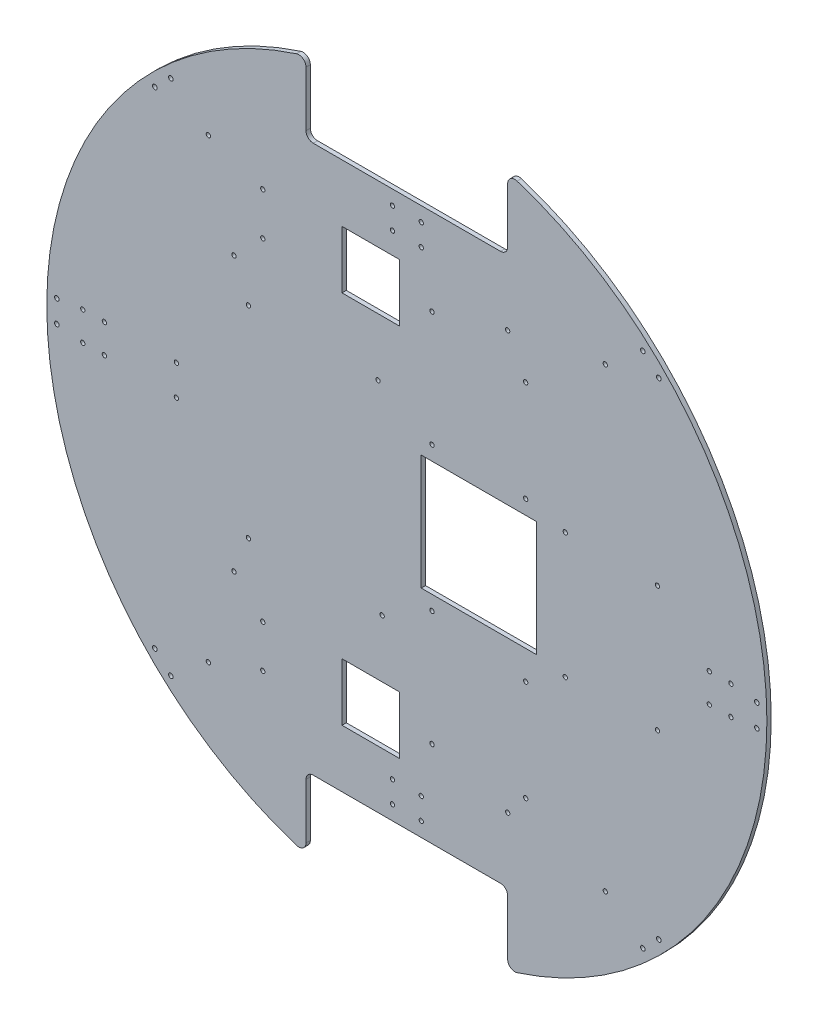
SolidWorks part; units mm, degrees
material "ｱｸﾘﾙ (中-上級の耐衝撃性)"
ref_plane "正面" through (0, 0, 0) normal (0, 0, 1) x (1, 0, 0)
ref_plane "平面" through (0, 0, 0) normal (0, 1, 0) x (1, 0, 0)
ref_plane "右側面" through (0, 0, 0) normal (1, 0, 0) x (0, 0, -1)
sketch "ｽｹｯﾁ1" plane through (0, 0, 0) normal (0, 0, 1) x (1, 0, 0)
  line L0 (0, -250) -> (0, 250) construction
  line L1 (-250, 0) -> (250, 0) construction
  circle A0 centre (0, 0) radius 250
  dimension "D1" = 500
extrude "ﾎﾞｽ - 押し出し1" add sketch "ｽｹｯﾁ1" against normal blind 3
sketch "ｽｹｯﾁ2" plane through (0, 0, 0) normal (0, 0, 1) x (1, 0, 0)
  line L0 (0, 250) -> (0, -250) construction
  line L1 (-250, 0) -> (250, 0) construction
  line L2 (0, 190) -> (52.533, 190) construction
  line L3 (0, 190) -> (-70, 190) construction
  line L5 (0, 190) -> (70, 190)
  line L7 (0, 250) -> (70, 250)
  line L8 (70, 190) -> (70, 250)
  line L9 (0, 190) -> (-70, 190)
  line L11 (0, 250) -> (-70, 250)
  line L12 (-70, 190) -> (-70, 250)
  circle A0 centre (0, 0) radius 250 construction
  dimension "D1" = 140
  dimension "D2" = 60
  dimension "D3" = 70
  dimension "D4" = 190
extrude "ｶｯﾄ - 押し出し1" cut sketch "ｽｹｯﾁ2" against normal through all
sketch "ｽｹｯﾁ3" plane through (0, 0, 0) normal (0, 0, 1) x (1, 0, 0)
  line L0 (0, 190) -> (0, -250) construction
  line L1 (-70, 190) -> (70, 190) construction
  line L2 (-250, 0) -> (250, 0) construction
  line L3 (-61.1353, -190) -> (70, -190) construction
  line L5 (0, -250) -> (70, -250)
  line L7 (0, -190) -> (70, -190)
  line L8 (70, -250) -> (70, -190)
  line L9 (0, -250) -> (-70, -250)
  line L11 (0, -190) -> (-70, -190)
  line L12 (-70, -250) -> (-70, -190)
  arc A0 (-70, 240) -> (70, 240) centre (0, 0) ccw construction
  dimension "D1" = 190
  dimension "D2" = 140
  dimension "D4" = 60
extrude "ｶｯﾄ - 押し出し2" cut sketch "ｽｹｯﾁ3" against normal through all
fillet "ﾌｨﾚｯﾄ1" radius 5 1 edges at (-70, 240, -1.5)
fillet "ﾌｨﾚｯﾄ2" radius 5 1 edges at (70, 240, -1.5)
fillet "ﾌｨﾚｯﾄ3" radius 5 1 edges at (70, 190, -1.5)
fillet "ﾌｨﾚｯﾄ4" radius 5 1 edges at (-70, 190, -1.5)
fillet "ﾌｨﾚｯﾄ5" radius 5 1 edges at (-70, -240, -1.5)
fillet "ﾌｨﾚｯﾄ6" radius 5 1 edges at (70, -190, -1.5)
fillet "ﾌｨﾚｯﾄ7" radius 5 1 edges at (70, -240, -1.5)
fillet "ﾌｨﾚｯﾄ8" radius 5 1 edges at (-70, -190, -1.5)
sketch "ｽｹｯﾁ18" plane through (0, 0, 0) normal (0, 0, 1) x (1, 0, 0)
  line L4 (0, 190) -> (0, -190) construction
  line L5 (-65, 190) -> (65, 190) construction
  line L6 (65, -190) -> (-65, -190) construction
  line L7 (0, 0) -> (-250, 0) construction
  line L8 (0, 130) -> (-213.5416, 130) construction
  line L9 (0, -130) -> (-213.5416, -130) construction
  circle A0 centre (-100, 144.75) radius 1.5
  circle A1 centre (-100, 115.25) radius 1.5
  circle A2 centre (-100, -115.25) radius 1.5
  circle A3 centre (-100, -144.75) radius 1.5
  arc A4 (-76.5306, 237.998) -> (-76.5306, -237.998) centre (0, 0) ccw construction
  dimension "D2" = 29.5
  dimension "D4" = 100
  dimension "D5" = 14.75
  dimension "D6" = 14.75
  dimension "D10" = 130
  dimension "D3" = 29.5
  dimension "D15" = 230.5
  dimension "D13" = 100
extrude "ｶｯﾄ - 押し出し10" cut sketch "ｽｹｯﾁ18" against normal through all
sketch "ｽｹｯﾁ19" plane through (0, 0, 0) normal (0, 0, 1) x (1, 0, 0)
  line L3 (0, 190) -> (0, -190) construction
  line L4 (-65, 190) -> (65, 190) construction
  line L5 (65, -190) -> (-65, -190) construction
  line L6 (0, 0) -> (-250, 0) construction
  circle A0 centre (-160, 10.5) radius 1.5
  circle A1 centre (-160, -10.5) radius 1.5
  arc A2 (-76.5306, 237.998) -> (-76.5306, -237.998) centre (0, 0) ccw construction
  dimension "D1" = 21
  dimension "D2" = 10.5
  dimension "D5" = 160
extrude "ｶｯﾄ - 押し出し11" cut sketch "ｽｹｯﾁ19" against normal blind 3
sketch "ｽｹｯﾁ20" plane through (0, 0, 0) normal (0, 0, 1) x (1, 0, 0)
  line L0 (0, 0) -> (-250, 0) construction
  line L1 (0, 0) -> (-174.2913, 179.2277) construction
  line L2 (0, 0) -> (-174.2913, -179.2277) construction
  line L4 (-250, 0) -> (-250, 106.5874) construction
  line L5 (-250, 0) -> (-250, -148.7336) construction
  circle A0 centre (-243, 7.75) radius 1.6
  circle A1 centre (-243, -7.75) radius 1.6
  circle A2 centre (-163.8551, 179.6123) radius 1.6
  circle A3 centre (-174.9672, 168.8062) radius 1.6
  circle A4 centre (-163.8551, -179.6123) radius 1.6
  circle A5 centre (-174.9672, -168.8062) radius 1.6
  arc A6 (-76.5306, 237.998) -> (-76.5306, -237.998) centre (0, 0) ccw construction
  dimension "D1" = 3.2
  dimension "D2" = 3.2
  dimension "D3" = 15.5
  dimension "D4" = 45.8
  dimension "D5" = 45.8
  dimension "D6" = 7
  dimension "D7" = 3.2
  dimension "D8" = 3.2
  dimension "D10" = 7.75
  dimension "D11" = 15.5
  dimension "D12" = 7.75
  dimension "D13" = 7.75
  dimension "D14" = 15.5
  dimension "D15" = 3.2
  dimension "D16" = 3.2
  dimension "D9" = 7
extrude "ｶｯﾄ - 押し出し12" cut sketch "ｽｹｯﾁ20" against normal through all
sketch "ｽｹｯﾁ21" plane through (0, 0, 0) normal (0, 0, 1) x (1, 0, 0)
  line L0 (-70, 200.2579) -> (-70, -195) construction
  line L1 (-70, 233.2381) -> (-70, 195) construction
  line L2 (70, 200.2579) -> (70, -203.5874) construction
  line L3 (70, 195) -> (70, 233.2381) construction
  line L4 (70, -233.2381) -> (70, -195) construction
  line L6 (250, 0) -> (250, 50.0378) construction
  line L7 (250, 0) -> (250, -56.1668) construction
  line L8 (0, 0) -> (199.5354, -229.4583) construction
  line L9 (0, 0) -> (186.4834, 214.449) construction
  line L10 (0, 0) -> (-164.0477, -188.6488) construction
  line L11 (0, 0) -> (-164.0477, 188.6488) construction
  line L12 (20.7556, 0) -> (-250, 0) construction
  line L13 (0, 0) -> (250, 0) construction
  arc A0 (76.5306, -237.998) -> (76.5306, 237.998) centre (0, 0) ccw construction
  arc A1 (-76.5306, 237.998) -> (-76.5306, -237.998) centre (0, 0) ccw construction
  circle A2 centre (137.8001, 158.465) radius 1.5
  circle A3 centre (137.8001, -158.465) radius 1.5
  circle A4 centre (-137.8001, -158.465) radius 1.5
  circle A5 centre (-137.8001, 158.465) radius 1.5
  dimension "D5" = 210
  dimension "D6" = 48.99
  dimension "D7" = 210
  dimension "D8" = 210
  dimension "D9" = 48.99
  dimension "D1" = 3
  dimension "D2" = 210
  dimension "D3" = 48.99
  dimension "D4" = 48.99
sketch "ｽｹｯﾁ24" plane through (0, 0, 0) normal (0, 0, 1) x (1, 0, 0)
  line L1 (250, 0) -> (250, 50.4715) construction
  line L2 (250, 0) -> (250, -52.0324) construction
  line L3 (0, 0) -> (250, 0) construction
  circle A0 centre (225, 10) radius 1.5
  circle A1 centre (225, -10) radius 1.5
  circle A2 centre (210, -10) radius 1.5
  circle A3 centre (210, 10) radius 1.5
  arc A4 (76.5306, -237.998) -> (76.5306, 237.998) centre (0, 0) ccw construction
  dimension "D1" = 15
  dimension "D2" = 20
  dimension "D9" = 25
extrude "ｶｯﾄ - 押し出し14" cut sketch "ｽｹｯﾁ24" against normal through all
sketch "ｽｹｯﾁ25" plane through (0, 0, 0) normal (0, 0, 1) x (1, 0, 0)
  line L2 (0, 0) -> (-250, 0) construction
  arc A0 (-76.5306, 237.998) -> (-76.5306, -237.998) centre (0, 0) ccw construction
  circle A1 centre (-225, 10) radius 1.5
  circle A2 centre (-225, -10) radius 1.5
  circle A3 centre (-210, -10) radius 1.5
  circle A4 centre (-210, 10) radius 1.5
  dimension "D3" = 15
  dimension "D2" = 20
  dimension "D1" = 10
extrude "ｶｯﾄ - 押し出し15" cut sketch "ｽｹｯﾁ25" against normal through all
extrude "ｶｯﾄ - 押し出し16" cut sketch "ｽｹｯﾁ21" against normal through all
sketch "ｽｹｯﾁ26" plane through (0, 0, 0) normal (0, 0, 1) x (1, 0, 0)
  line L0 (0, 0) -> (250, 0) construction
  line L1 (0, 0) -> (174.2913, 179.2277) construction
  line L2 (0, 0) -> (174.2913, -179.2277) construction
  line L3 (250, 0) -> (250, -77.1095) construction
  line L4 (250, 0) -> (250, 74.9851) construction
  line L5 (174.2913, 179.2277) -> (142.4135, 210.2274) construction
  line L6 (174.2913, 179.2277) -> (219.1124, 135.641) construction
  line L7 (174.2913, -179.2277) -> (133.8059, -218.598) construction
  line L8 (169.1818, -184.1964) -> (198.6309, -155.5584) construction
  arc A0 (76.5306, -237.998) -> (76.5306, 237.998) centre (0, 0) ccw construction
  circle A1 centre (174.9672, -168.8062) radius 1.6
  circle A2 centre (163.8551, -179.6123) radius 1.6
  circle A3 centre (243, -7.75) radius 1.6
  circle A4 centre (243, 7.75) radius 1.6
  circle A5 centre (174.9672, 168.8062) radius 1.6
  circle A6 centre (163.8551, 179.6123) radius 1.6
  dimension "D3" = 15.5
  dimension "D5" = 7.75
  dimension "D6" = 15.5
  dimension "D7" = 3.2
  dimension "D8" = 3.2
  dimension "D9" = 7
  dimension "D10" = 7
  dimension "D11" = 7
  dimension "D12" = 7
  dimension "D13" = 3.2
  dimension "D14" = 3.2
  dimension "D15" = 90
  dimension "D16" = 7.75
  dimension "D17" = 15.5
  dimension "D18" = 7
  dimension "D19" = 3.2
  dimension "D20" = 3.2
  dimension "D4" = 7.75
  dimension "D21" = 7
  dimension "D1" = 45.8
  dimension "D2" = 45.8
extrude "ｶｯﾄ - 押し出し17" cut sketch "ｽｹｯﾁ26" against normal through all
sketch "ｽｹｯﾁ27" plane through (0, 0, 0) normal (0, 0, 1) x (1, 0, 0)
  line L0 (0, 190) -> (0, -190) construction
  line L1 (65, -190) -> (-65, -190) construction
  line L3 (-65, 190) -> (65, 190) construction
  circle A0 centre (-10, 180) radius 1.5
  circle A1 centre (10, 180) radius 1.5
  circle A2 centre (10, 165) radius 1.5
  circle A3 centre (-10, 165) radius 1.5
  circle A4 centre (10, -180) radius 1.5
  circle A5 centre (10, -165) radius 1.5
  circle A6 centre (-10, -165) radius 1.5
  circle A7 centre (-10, -180) radius 1.5
  dimension "D12" = 10
  dimension "D20" = 10
extrude "ｶｯﾄ - 押し出し18" cut sketch "ｽｹｯﾁ27" against normal through all
sketch "ｽｹｯﾁ28" plane through (0, 0, 0) normal (0, 0, 1) x (1, 0, 0)
  line L0 (-250, 0) -> (250, 0) construction
  line L1 (50, 156.965) -> (50, -156.965) construction
  line L2 (0, 190) -> (0, -190) construction
  line L3 (-65, 190) -> (65, 190) construction
  line L4 (65, -190) -> (-65, -190) construction
  line L5 (10, 40) -> (90, 40)
  line L8 (90, -40) -> (10, -40)
  line L9 (10, 1.028) -> (10, -40)
  line L13 (10, 1.028) -> (10, 40)
  line L17 (90, 0) -> (90, 40)
  line L21 (90, 0) -> (90, -40)
  arc A0 (-76.5306, 237.998) -> (-76.5306, -237.998) centre (0, 0) ccw construction
  arc A1 (76.5306, -237.998) -> (76.5306, 237.998) centre (0, 0) ccw construction
  circle A4 centre (17.5, 130) radius 1.5
  circle A5 centre (82.5, 120) radius 1.5
  circle A6 centre (17.5, 50) radius 1.5
  circle A7 centre (82.5, 50) radius 1.5
  circle A8 centre (17.5, -50) radius 1.5
  circle A9 centre (82.5, -60) radius 1.5
  circle A10 centre (17.5, -130) radius 1.5
  circle A11 centre (82.5, -130) radius 1.5
  dimension "D3" = 60
  dimension "D4" = 80
  dimension "D5" = 50
  dimension "D12" = 80
  dimension "D15" = 70
  dimension "D6" = 65
  dimension "D7" = 80
  dimension "D29" = 50
extrude "ｶｯﾄ - 押し出し19" cut sketch "ｽｹｯﾁ28" against normal through all
sketch "ｽｹｯﾁ29" plane through (0, 0, 0) normal (0, 0, 1) x (1, 0, 0)
  line L0 (-65, 190) -> (65, 190) construction
  line L1 (-45, -110) -> (-5, -110)
  line L2 (-45, -110) -> (-45, -150)
  line L3 (-45, -150) -> (-5, -150)
  line L4 (-5, -110) -> (-5, -150)
  line L5 (-45, 150) -> (-5, 150)
  line L6 (-45, 150) -> (-45, 110)
  line L7 (-45, 110) -> (-5, 110)
  line L8 (-5, 150) -> (-5, 110)
  line L10 (-70, 209.1356) -> (-70, -208.363) construction
  line L11 (-70, 233.2381) -> (-70, 195) construction
  line L12 (-70, -195) -> (-70, -233.2381) construction
  dimension "D1" = 40
  dimension "D5" = 40
  dimension "D6" = 40
  dimension "D7" = 25
extrude "ｶｯﾄ - 押し出し20" cut sketch "ｽｹｯﾁ29" against normal through all
sketch "ｽｹｯﾁ30" plane through (0, 0, 0) normal (0, 0, 1) x (1, 0, 0)
  line L0 (-250, 0) -> (250, 0) construction
  line L1 (0, 190) -> (0, -190) construction
  line L4 (-65, 190) -> (65, 190) construction
  line L5 (65, -190) -> (-65, -190) construction
  arc A0 (-76.5306, 237.998) -> (-76.5306, -237.998) centre (0, 0) ccw construction
  arc A1 (76.5306, -237.998) -> (76.5306, 237.998) centre (0, 0) ccw construction
  circle A2 centre (110, 43.5) radius 1.5
  circle A3 centre (174, 43.5) radius 1.5
  circle A4 centre (110, -43.5) radius 1.5
  circle A5 centre (174, -43.5) radius 1.5
  dimension "D1" = 87
  dimension "D2" = 110
  dimension "D3" = 64
  dimension "D4" = 64
  dimension "D5" = 43.5
extrude "ｶｯﾄ - 押し出し21" cut sketch "ｽｹｯﾁ30" against normal through all
sketch "ｽｹｯﾁ31" plane through (0, 0, 0) normal (0, 0, 1) x (1, 0, 0)
  line L0 (-250, 0) -> (7.1019, 0) construction
  line L1 (0, 190) -> (0, -190) construction
  line L2 (-65, 190) -> (65, 190) construction
  line L3 (65, -190) -> (-65, -190) construction
  arc A0 (-76.5306, 237.998) -> (-76.5306, -237.998) centre (0, 0) ccw construction
  circle A1 centre (-20, 70) radius 1.5
  circle A2 centre (-110, 70) radius 1.5
  circle A3 centre (-110, -70) radius 1.5
  circle A4 centre (-17.141, -70) radius 1.5
  dimension "D1" = 140
  dimension "D2" = 20
  dimension "D8" = 90
extrude "ｶｯﾄ - 押し出し22" cut sketch "ｽｹｯﾁ31" against normal through all
sketch "ｽｹｯﾁ32" plane through (0, 0, 0) normal (0, 0, 1) x (1, 0, 0)
  line L0 (0, 190) -> (0, -190) construction
  line L1 (-65, 190) -> (65, 190) construction
  line L2 (65, -190) -> (-65, -190) construction
  line L3 (-250, 0) -> (250, 0) construction
  line L4 (70, 209.7769) -> (70, -203.5409) construction
  arc A0 (-76.5306, 237.998) -> (-76.5306, -237.998) centre (0, 0) ccw construction
  arc A1 (76.5306, -237.998) -> (76.5306, 237.998) centre (0, 0) ccw construction
  circle A2 centre (-120, 95) radius 1.5
  circle A3 centre (-120, -95) radius 1.5
  circle A4 centre (70, 145) radius 1.5
  circle A5 centre (70, -145) radius 1.5
  dimension "D1" = 95
  dimension "D2" = 95
  dimension "D4" = 120
  dimension "D5" = 70
  dimension "D6" = 70
  dimension "D7" = 145
  dimension "D13" = 145
  dimension "D3" = 120
extrude "ｶｯﾄ - 押し出し23" cut sketch "ｽｹｯﾁ32" against normal through all
